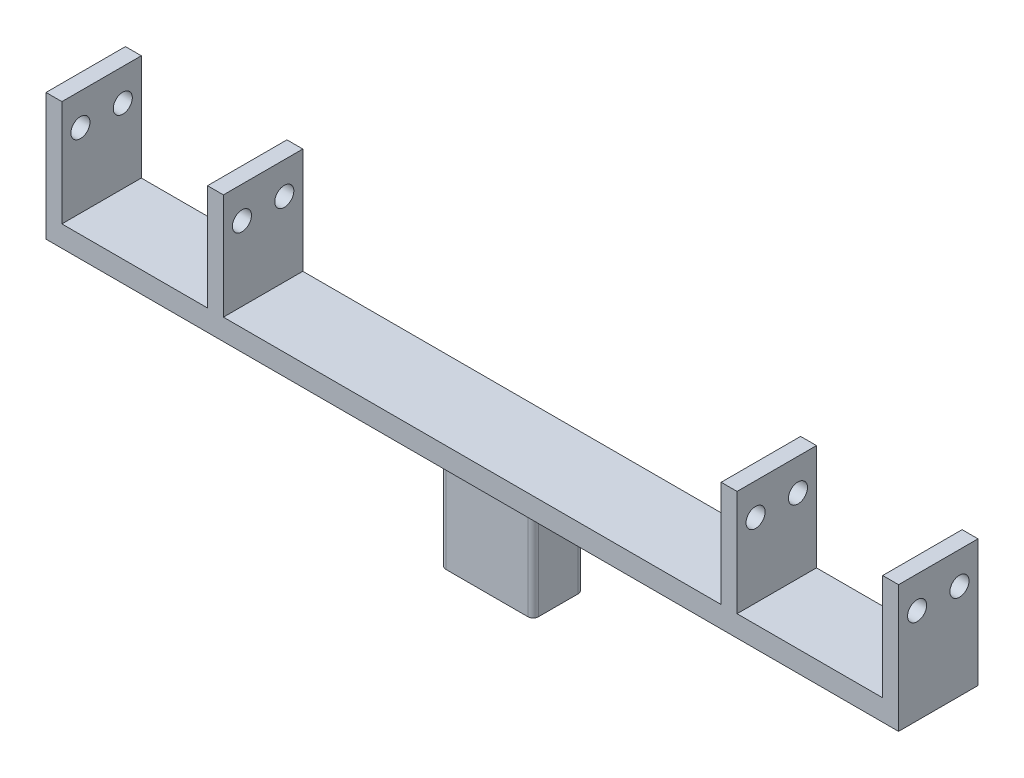
SolidWorks part; units mm, degrees
ref_plane "Front Plane" through (0, 0, 0) normal (0, 0, 1) x (1, 0, 0)
ref_plane "Top Plane" through (0, 0, 0) normal (0, 1, 0) x (1, 0, 0)
ref_plane "Right Plane" through (0, 0, 0) normal (1, 0, 0) x (0, 0, -1)
sketch "Sketch1" plane through (0, 0, 0) normal (0, 1, 0) x (1, 0, 0)
  line L0 (0, 0) -> (18.0146, 0) construction
  line L1 (18.0146, 0) -> (-21.4236, 0) construction
  line L2 (0, 0) -> (0, 10.5375) construction
  line L3 (0, 10.5375) -> (0, -15.3064) construction
  line L5 (-80.5, -7.5) -> (80.5, -7.5)
  line L6 (-80.5, -7.5) -> (-80.5, 7.5)
  line L7 (-80.5, 7.5) -> (80.5, 7.5)
  line L8 (80.5, -7.5) -> (80.5, 7.5)
  line L9 (-80.5, -7.5) -> (80.5, 7.5) construction
  line L10 (-80.5, 7.5) -> (80.5, -7.5) construction
  dimension "D1" = 15
  dimension "D2" = 161
extrude "Boss-Extrude1" add sketch "Sketch1" along normal blind 4
sketch "Sketch2" plane through (0, 4, 0) normal (0, 1, 0) x (1, 0, 0)
  line L0 (0, 0) -> (0, 39.5664) construction
  line L1 (0, 39.5664) -> (0, -35.4827) construction
  line L2 (0, 0) -> (92.9451, 0) construction
  line L3 (92.9451, 0) -> (-105.1256, 0) construction
  line L4 (80.5, 7.5) -> (-80.5, 7.5) construction
  line L5 (-50, 7.5) -> (-47, 7.5)
  line L6 (-50, 7.5) -> (-50, -7.5)
  line L7 (-50, -7.5) -> (-47, -7.5)
  line L8 (-47, 7.5) -> (-47, -7.5)
  line L9 (-80.5, -7.5) -> (80.5, -7.5) construction
  line L11 (-80.5, 7.5) -> (-77.5, 7.5)
  line L12 (-80.5, 7.5) -> (-80.5, -7.5)
  line L13 (-80.5, -7.5) -> (-77.5, -7.5)
  line L14 (-77.5, 7.5) -> (-77.5, -7.5)
  line L15 (80.5, 7.5) -> (77.5, 7.5)
  line L16 (80.5, 7.5) -> (80.5, -7.5)
  line L17 (80.5, -7.5) -> (77.5, -7.5)
  line L18 (77.5, 7.5) -> (77.5, -7.5)
  line L19 (50, 7.5) -> (47, 7.5)
  line L20 (50, 7.5) -> (50, -7.5)
  line L21 (50, -7.5) -> (47, -7.5)
  line L22 (47, 7.5) -> (47, -7.5)
  dimension "D1" = 3
  dimension "D2" = 50
  dimension "D3" = 50
extrude "Boss-Extrude2" add sketch "Sketch2" along normal blind 20
sketch "Sketch4" plane through (-80.5, 0, 0) normal (-1, 0, 0) x (0, 0, 1)
  line L0 (0, 0) -> (0, 38.315) construction
  line L1 (-7.5, 0) -> (7.5, 0) construction
  line L2 (0, 0) -> (16.3936, 0) construction
  line L3 (0, 0) -> (-17.8484, 0) construction
  circle A0 centre (4, 18) radius 1.8
  circle A1 centre (-4, 18) radius 1.8
  dimension "D1" = 3.6
  dimension "D2" = 18
  dimension "D3" = 4
extrude "Cut-Extrude2" cut sketch "Sketch4" against normal through all both and the other way through all
sketch "Sketch5" plane through (0, 0, 0) normal (0, -1, 0) x (1, 0, 0)
  line L1 (-7.75, -4.75) -> (7.75, -4.75)
  line L2 (-8.75, -3.75) -> (-8.75, 3.75)
  line L3 (-7.75, 4.75) -> (7.75, 4.75)
  line L4 (8.75, -3.75) -> (8.75, 3.75)
  line L5 (-8.75, -4.75) -> (8.75, 4.75) construction
  line L6 (-8.75, 4.75) -> (8.75, -4.75) construction
  arc A0 (-8.75, 3.75) -> (-7.75, 4.75) centre (-7.75, 3.75) cw
  arc A1 (8.75, 3.75) -> (7.75, 4.75) centre (7.75, 3.75) ccw
  arc A2 (8.75, -3.75) -> (7.75, -4.75) centre (7.75, -3.75) cw
  arc A3 (-7.75, -4.75) -> (-8.75, -3.75) centre (-7.75, -3.75) cw
  point P0 (0, 0)
  dimension "D3" = 1
  dimension "D4" = 1
  dimension "D5" = 1
  dimension "D6" = 1
  dimension "D1" = 9.5
  dimension "D2" = 17.5
extrude "Boss-Extrude3" add sketch "Sketch5" along normal blind 19
